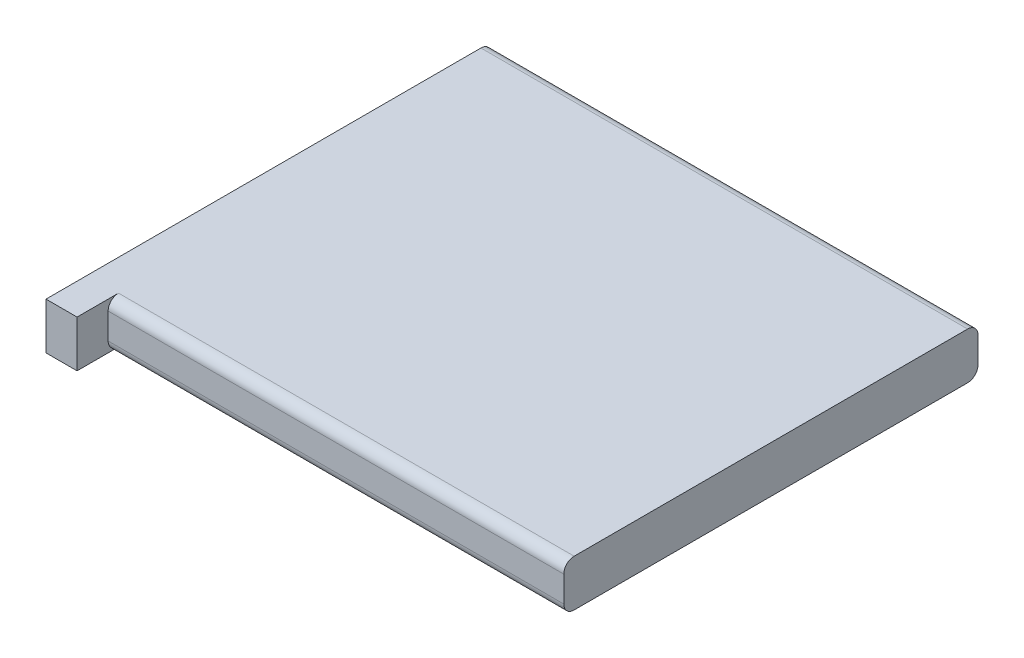
SolidWorks part; units mm, degrees
ref_plane "Front Plane" through (0, 0, 0) normal (0, 0, 1) x (1, 0, 0)
ref_plane "Top Plane" through (0, 0, 0) normal (0, 1, 0) x (1, 0, 0)
ref_plane "Right Plane" through (0, 0, 0) normal (1, 0, 0) x (0, 0, -1)
sketch "Sketch1" plane through (0, 0, 0) normal (0, 1, 0) x (1, 0, 0)
  line L1 (23.5, -20) -> (-23.5, -20)
  line L2 (23.5, -20) -> (23.5, 20)
  line L3 (23.5, 20) -> (-23.5, 20)
  line L4 (-23.5, -20) -> (-23.5, 20)
  line L5 (23.5, -20) -> (-23.5, 20) construction
  line L6 (23.5, 20) -> (-23.5, -20) construction
  point P0 (0, 0)
  dimension "D1" = 47
  dimension "D2" = 40
extrude "Boss-Extrude1" add sketch "Sketch1" along normal blind 4.5
fillet "Fillet1" radius 1 4 edges at (0, 0, -20) (0, 4.5, -20) (0, 0, 20) (0, 4.5, 20)
sketch "Sketch2" plane through (0, 0, 20) normal (0, 0, 1) x (1, 0, 0)
  line L0 (23.5, 0) -> (-23.5, 0) construction
  line L1 (-23.5, 4.5) -> (-20.5, 4.5)
  line L2 (-23.5, 4.5) -> (-23.5, 0)
  line L3 (-23.5, 0) -> (-20.5, 0)
  line L4 (-20.5, 4.5) -> (-20.5, 0)
  dimension "D1" = 3
extrude "Boss-Extrude2" add sketch "Sketch2" along normal blind 3 and the other way blind 3
